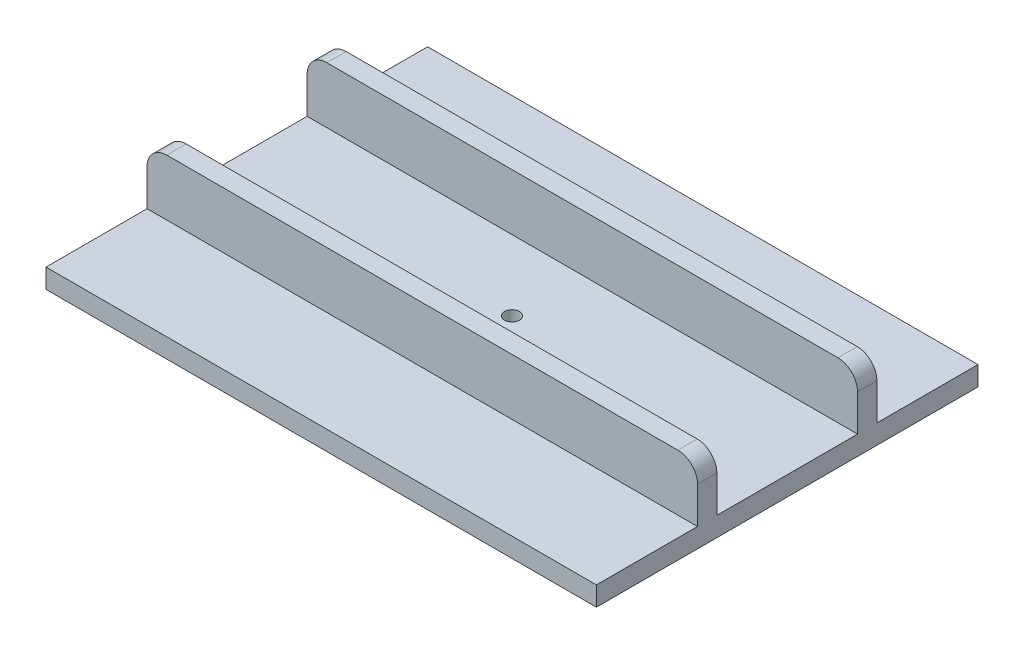
SolidWorks part; units mm, degrees
material "Acrylic (Medium-high impact)"
ref_plane "Front Plane" through (0, 0, 0) normal (0, 0, 1) x (1, 0, 0)
ref_plane "Top Plane" through (0, 0, 0) normal (0, 1, 0) x (1, 0, 0)
ref_plane "Right Plane" through (0, 0, 0) normal (1, 0, 0) x (0, 0, -1)
sketch "Sketch1" plane through (0, 0, 0) normal (0, 1, 0) x (1, 0, 0)
  line L1 (-248.412, -172.212) -> (248.412, -172.212)
  line L2 (-248.412, -172.212) -> (-248.412, 172.212)
  line L3 (-248.412, 172.212) -> (248.412, 172.212)
  line L4 (248.412, -172.212) -> (248.412, 172.212)
  line L5 (-248.412, -172.212) -> (248.412, 172.212) construction
  line L6 (-248.412, 172.212) -> (248.412, -172.212) construction
  point P0 (0, 0)
  dimension "D1" = 496.824
  dimension "D2" = 344.424
extrude "Boss-Extrude1" add sketch "Sketch1" along normal blind 17.4625
sketch "Sketch3" plane through (0, 17.4625, 0) normal (0, 1, 0) x (1, 0, 0)
  circle A0 centre (0, 0) radius 6.7627
  dimension "D1" = 13.5255
extrude "Cut-Extrude1" cut sketch "Sketch3" against normal up to next
sketch "Sketch5" plane through (0, 17.4625, 0) normal (0, 1, 0) x (1, 0, 0)
  line L0 (-248.412, 172.212) -> (-248.412, -172.212) construction
  line L1 (-248.412, 80.9625) -> (248.412, 80.9625)
  line L2 (-248.412, 80.9625) -> (-248.412, 63.5)
  line L3 (-248.412, 63.5) -> (248.412, 63.5)
  line L4 (248.412, 80.9625) -> (248.412, 63.5)
  line L5 (248.412, -172.212) -> (248.412, 172.212) construction
  dimension "D1" = 63.5
  dimension "D2" = 17.4625
extrude "Boss-Extrude2" add sketch "Sketch5" along normal blind 50.8
mirror "Mirror1" about plane through (0, 0, 0) normal (0, 0, 1) of "Boss-Extrude2"
fillet "Fillet2" radius 17.78 4 edges at (248.412, 68.2625, -72.2313) (248.412, 68.2625, 72.2313) (-248.412, 68.2625, 72.2313) (-248.412, 68.2625, -72.2313)
